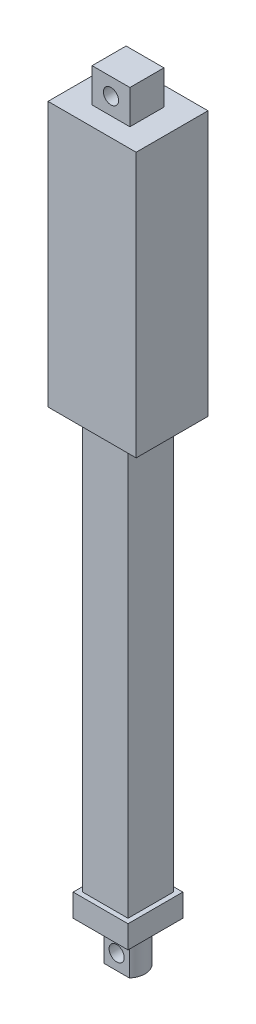
SolidWorks part; units mm, degrees
ref_plane "前视基准面" through (0, 0, 0) normal (0, 0, 1) x (1, 0, 0)
ref_plane "上视基准面" through (0, 0, 0) normal (0, 1, 0) x (1, 0, 0)
ref_plane "右视基准面" through (0, 0, 0) normal (1, 0, 0) x (0, 0, -1)
sketch "草图1" plane through (0, 0, 0) normal (0, 1, 0) x (1, 0, 0)
  line L1 (-11.65, 9.5) -> (11.65, 9.5)
  line L2 (-11.65, 9.5) -> (-11.65, -9.5)
  line L3 (-11.65, -9.5) -> (11.65, -9.5)
  line L4 (11.65, 9.5) -> (11.65, -9.5)
  line L5 (0, -9.5) -> (0, 9.5) construction
  line L6 (-11.65, 0) -> (11.65, 0) construction
  point P0 (0, 0)
  dimension "D1" = 19
  dimension "D2" = 23.3
extrude "凸台-拉伸1" add sketch "草图1" along normal blind 70
sketch "草图2" plane through (0, 70, 0) normal (0, 1, 0) x (1, 0, 0)
  line L1 (-5, 4.5) -> (5, 4.5)
  line L2 (-5, 4.5) -> (-5, -4.5)
  line L3 (-5, -4.5) -> (5, -4.5)
  line L4 (5, 4.5) -> (5, -4.5)
  line L5 (0, -4.5) -> (0, 4.5) construction
  line L6 (-5, 0) -> (5, 0) construction
  point P0 (0, 0)
  dimension "D1" = 10
  dimension "D2" = 9
extrude "凸台-拉伸2" add sketch "草图2" along normal blind 9
sketch "草图3" plane through (0, 0, 4.5) normal (0, 0, 1) x (1, 0, 0)
  line L0 (-5, 74.5) -> (5, 74.5) construction
  line L1 (-5, 79) -> (-5, 70) construction
  line L2 (5, 79) -> (5, 70) construction
  circle A0 centre (0, 74.5) radius 2
  dimension "D1" = 4
extrude "切除-拉伸1" cut sketch "草图3" against normal through all both and the other way through all
sketch "草图4" plane through (0, 0, 0) normal (0, -1, 0) x (1, 0, 0)
  line L1 (-6, 6) -> (6, 6)
  line L2 (-6, 6) -> (-6, -6)
  line L3 (-6, -6) -> (6, -6)
  line L4 (6, 6) -> (6, -6)
  line L5 (0, -6) -> (0, 6) construction
  line L6 (-6, 0) -> (6, 0) construction
  point P0 (0, 0)
  dimension "D1" = 12
  dimension "D2" = 12
extrude "凸台-拉伸3" add sketch "草图4" along normal blind 110
sketch "草图5" plane through (0, -110, 0) normal (0, -1, 0) x (1, 0, 0)
  line L1 (-7.25, 7.25) -> (7.25, 7.25)
  line L2 (-7.25, 7.25) -> (-7.25, -7.25)
  line L3 (-7.25, -7.25) -> (7.25, -7.25)
  line L4 (7.25, 7.25) -> (7.25, -7.25)
  line L5 (0, -7.25) -> (0, 7.25) construction
  line L6 (-7.25, 0) -> (7.25, 0) construction
  point P0 (0, 0)
  dimension "D1" = 14.5
  dimension "D2" = 14.5
extrude "凸台-拉伸4" add sketch "草图5" along normal blind 6
sketch "草图6" plane through (0, -116, 0) normal (0, -1, 0) x (1, 0, 0)
  circle A0 centre (0, 0) radius 4.5
  dimension "D1" = 9
extrude "凸台-拉伸5" add sketch "草图6" along normal blind 10.5
sketch "草图7" plane through (0, -126.5, 0) normal (0, -1, 0) x (1, 0, 0)
  line L0 (-4.5, 0) -> (4.5, 0) construction
  line L1 (-3.3541, -3) -> (3.3541, -3)
  line L2 (-3.3541, 3) -> (3.3541, 3)
  line L3 (-11.1028, -3) -> (11.2704, -3) construction
  line L4 (-11.1028, 0) -> (11.2704, 0) construction
  line L5 (-11.1028, 3) -> (11.2704, 3) construction
  arc A0 (-3.3541, -3) -> (3.3541, -3) centre (0, 0) ccw
  circle A1 centre (0, 0) radius 4.5
  arc A2 (3.3541, 3) -> (-3.3541, 3) centre (0, 0) ccw
  dimension "D1" = 3
  dimension "D2" = 3
  dimension "D3" = 0
extrude "切除-拉伸3" cut sketch "草图7" against normal up to surface (10.5 mm away) contours A2 L2 | L1 A0 up to face at (0, -116, -4.5)
sketch "草图8" plane through (0, 0, -3) normal (0, 0, -1) x (-1, 0, 0)
  line L0 (0, -126.5) -> (0, -116) construction
  line L1 (3.3541, -126.5) -> (-3.3541, -126.5) construction
  line L2 (-3.3541, -116) -> (3.3541, -116) construction
  circle A0 centre (0, -122.5) radius 2
  dimension "D1" = 4
  dimension "4" = 4
extrude "切除-拉伸4" cut sketch "草图8" against normal through all
equation "\"、\"=9"
